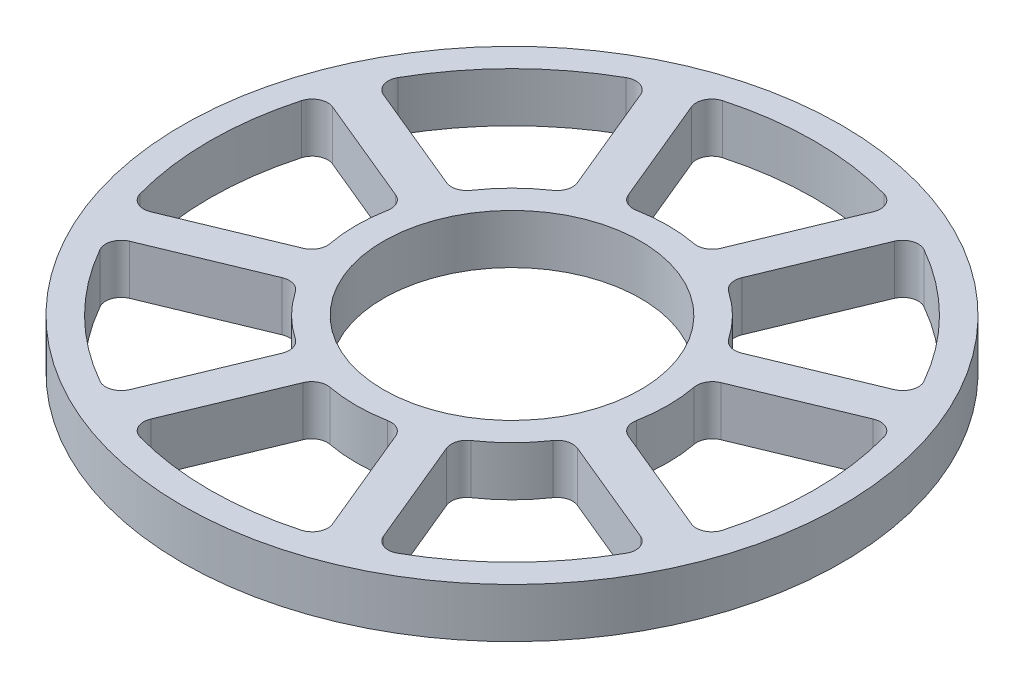
SolidWorks part; units mm, degrees
material "6061-T6 (SS)"
ref_plane "Front Plane" through (0, 0, 0) normal (0, 0, 1) x (1, 0, 0)
ref_plane "Top Plane" through (0, 0, 0) normal (0, 1, 0) x (1, 0, 0)
ref_plane "Right Plane" through (0, 0, 0) normal (1, 0, 0) x (0, 0, -1)
sketch "Sketch2" plane through (0, 0, 0) normal (1, 0, 0) x (0, 0, -1)
  line L0 (0, 0) -> (-82.55, 0)
  line L1 (-82.55, 0) -> (-82.55, 12.7)
  line L2 (-82.55, 12.7) -> (0, 12.7)
  line L5 (0, 12.7) -> (0, 0)
  dimension "D1" = 82.55
  dimension "D2" = 12.7
ref_axis "Axis1" through (0, -0.5, 0) along (0, 1, 0)
revolve "Revolve1" add sketch "Sketch2" angle 360 about axis through (0, -0.5, 0) along (0, 1, 0)
hole_wizard "#6-32 Tapped Hole1" [suppressed] positions "Sketch6" profile "Sketch7" tap size "#6-32" standard "ANSI Inch"
sketch "Sketch6" plane through (0, 12.7, 0) normal (0, 1, 0) x (1, 0, 0)
  line L0 (0, 0) -> (-53.438, 129.0108) construction
  line L2 (0, 0) -> (0, 109.0908) construction
  line L3 (0, 0) -> (-76.2663, 31.5905) construction
  line L4 (0, 0) -> (-68.4315, 68.4315) construction
  circle A0 centre (0, 0) radius 82.55 construction
  point P0 (-27.7637, 67.0275)
  point P18 (-61.1608, 25.3336)
  point P27 (-25.4558, 25.4558)
  dimension "D1" = 22.5
  dimension "D2" = 72.55
  dimension "D3" = 45
  dimension "D4" = 66.2
  dimension "D6" = 22.5
  dimension "D5" = 36
sketch "Sketch7" plane through (-27.7637, 12.7, -67.0275) normal (1, 0, 0) x (0, 0, 1)
  line L0 (0, 0) -> (0, 12.7)
  line L1 (0, 12.7) -> (1.3525, 12.7)
  line L2 (1.3525, 12.7) -> (1.3525, 0)
  line L5 (1.3525, 0) -> (0, 0)
  line L11 (0, -6.35) -> (0, 107.95) construction
  dimension "Thread Major Dia." = 2.7051
  dimension "Thru Tap Drill Depth" = 12.7
pattern_circular "CirPattern3" [suppressed] count 4 over 360 about axis through (0, -0.5, 0) along (0, 1, 0)
sketch "Sketch8" plane through (0, 12.7, 0) normal (0, 1, 0) x (1, 0, 0)
  line L4 (0, 0) -> (0, 93.9995) construction
  line L5 (0, 0) -> (113.8372, 0) construction
  line L6 (-10.5679, 38.5787) -> (-24.996, 73.4112)
  line L7 (10.5679, 38.5787) -> (24.996, 73.4112)
  line L8 (0, 0) -> (-27.7637, 67.0275) construction
  arc A0 (-10.5679, 38.5787) -> (10.5679, 38.5787) centre (0, 0) cw
  arc A1 (-24.996, 73.4112) -> (24.996, 73.4112) centre (0, 0) cw
  circle A2 centre (0, 0) radius 82.55 construction
  dimension "D1" = 40
  dimension "D2" = 5
  dimension "D3" = 5
  dimension "D4" = 22.5
extrude "Cut-Extrude1" cut sketch "Sketch8" against normal through all
fillet "Fillet1" radius 4 4 edges at (10.5679, 6.35, -38.5787) (24.996, 6.35, -73.4112) (-10.5679, 6.35, -38.5787) (-24.996, 6.35, -73.4112)
pattern_circular "CirPattern4" count 8 over 360 about axis through (0, 0, 0) along (0, 1, 0) of "Cut-Extrude1", "Fillet1"
chamfer "Chamfer2" [suppressed] distance 1 angle 45
sketch "Sketch9" plane through (0, 12.7, 0) normal (0, 1, 0) x (1, 0, 0)
  circle A0 centre (0, 0) radius 33
  dimension "D1" = 66
extrude "Cut-Extrude2" cut sketch "Sketch9" against normal through all
sketch "Sketch10" plane through (0, 0, 0) normal (0, 1, 0) x (1, 0, 0)
  circle A0 centre (0, 0) radius 84.55
  circle A1 centre (0, 0) radius 82.55
  circle A2 centre (0, 0) radius 82.55 construction
  dimension "D1" = 2
extrude "Boss-Extrude1" add sketch "Sketch10" along normal blind 12.7
equation "\"TubeDiameter\" = 6.500in"
equation "\"D1@Sketch2\"=\"TubeDiameter\"/2"
equation "\"D2@Sketch6\"=\"TubeDiameter\"/2-10mm"
